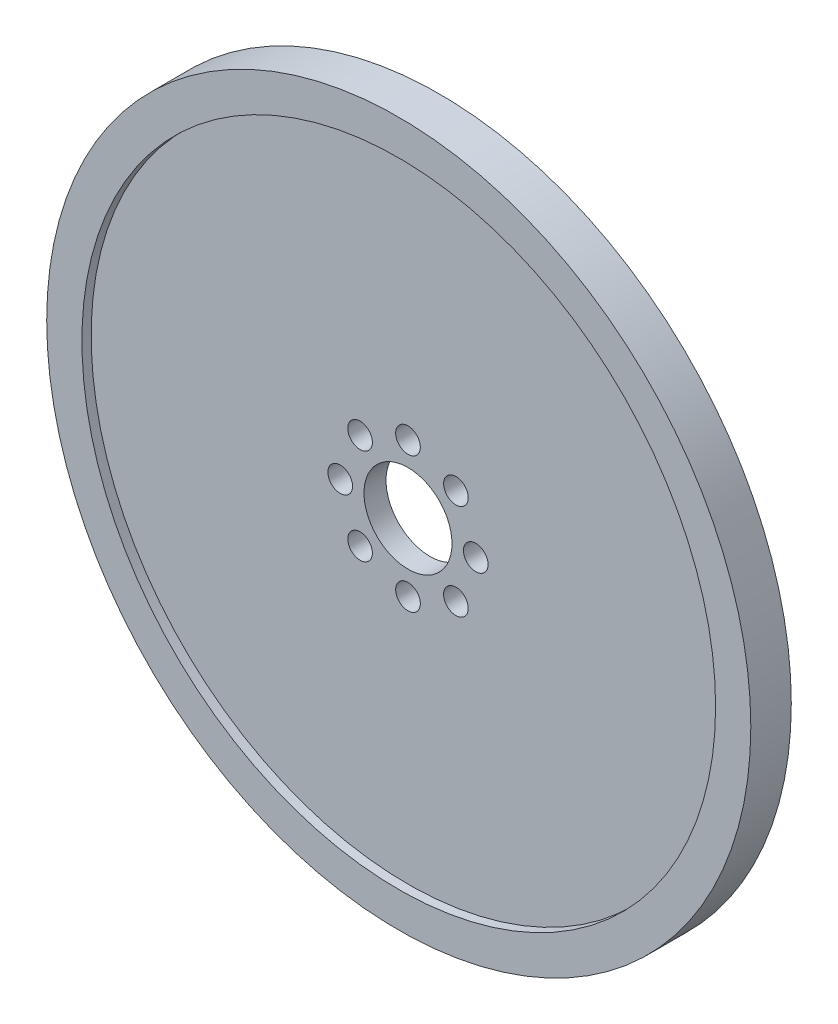
SolidWorks part; units mm, degrees
ref_plane "Front Plane" through (0, 0, 0) normal (0, 0, 1) x (1, 0, 0)
ref_plane "Top Plane" through (0, 0, 0) normal (0, 1, 0) x (1, 0, 0)
ref_plane "Right Plane" through (0, 0, 0) normal (1, 0, 0) x (0, 0, -1)
sketch "Sketch1" plane through (0, 0, 0) normal (0, 0, 1) x (1, 0, 0)
  circle A0 centre (0, 0) radius 50.8
  circle A1 centre (0, 0) radius 45.72
  dimension "D1" = 101.6
  dimension "D2" = 91.44
extrude "Boss-Extrude1" add sketch "Sketch1" along normal mid plane 5.842
sketch "Sketch3" plane through (0, 0, 0) normal (0, 0, 1) x (1, 0, 0)
  circle A0 centre (0, 0) radius 45.72
  circle A1 centre (0, 0) radius 6.35
  circle A2 centre (0, 9.779) radius 1.778
  circle A3 centre (6.9148, 6.9148) radius 1.778
  circle A4 centre (9.779, 0) radius 1.778
  circle A5 centre (6.9148, -6.9148) radius 1.778
  circle A6 centre (0, -9.779) radius 1.778
  circle A7 centre (-6.9148, -6.9148) radius 1.778
  circle A8 centre (-9.779, 0) radius 1.778
  circle A9 centre (-6.9148, 6.9148) radius 1.778
  dimension "D1" = 12.7
  dimension "D2" = 3.556
  dimension "D5" = 91.44
  dimension "D3" = 9.779
  dimension "D4" = 8
extrude "Boss-Extrude2" add sketch "Sketch3" along normal mid plane 3.175
